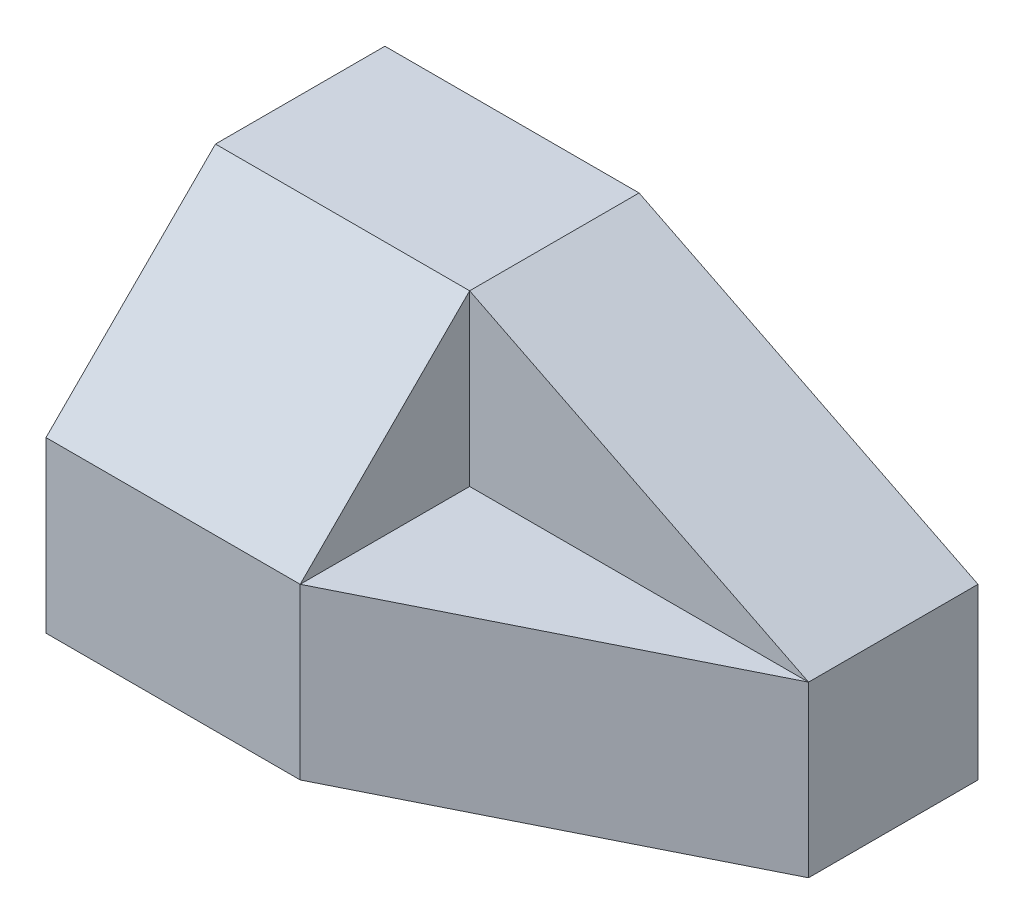
SolidWorks part; units mm, degrees
ref_plane "Front Plane" through (0, 0, 0) normal (0, 0, 1) x (1, 0, 0)
ref_plane "Top Plane" through (0, 0, 0) normal (0, 1, 0) x (1, 0, 0)
ref_plane "Right Plane" through (0, 0, 0) normal (1, 0, 0) x (0, 0, -1)
sketch "Sketch1" plane through (0, 0, 0) normal (0, 1, 0) x (1, 0, 0)
  line L1 (0, 0) -> (177.8, 0)
  line L2 (0, 0) -> (0, 101.6)
  line L3 (0, 101.6) -> (177.8, 101.6)
  line L4 (177.8, 0) -> (177.8, 101.6)
extrude "Boss-Extrude1" add sketch "Sketch1" along normal blind 101.6
sketch "Sketch2" plane through (0, 0, 0) normal (-1, 0, 0) x (0, 0, 1)
  line L1 (-101.6, 101.6) -> (0, 101.6) construction
  line L3 (0, 101.6) -> (0, 0) construction
  line L4 (0, 50.8) -> (-50.8, 101.6)
  line L5 (-50.8, 101.6) -> (0, 101.6)
extrude "Cut-Extrude7" cut sketch "Sketch2" against normal blind 76.2 and the other way through all flip side to cut
sketch "Sketch6" plane through (0, 0, 0) normal (0, 1, 0) x (1, 0, 0)
  line L0 (76.2, 0) -> (177.8, 50.8)
  line L1 (177.8, 0) -> (177.8, 101.6) construction
  line L2 (177.8, 50.8) -> (177.8, 0)
  line L3 (177.8, 0) -> (76.2, 0)
extrude "Cut-Extrude10" cut sketch "Sketch6" along normal blind 50.8
sketch "Sketch7" plane through (177.8, 0, 0) normal (1, 0, 0) x (0, 0, -1)
  line L0 (0, 50.8) -> (50.8, 101.6)
  line L1 (0, 101.6) -> (101.6, 101.6) construction
  line L2 (50.8, 101.6) -> (50.8, 50.8)
  line L3 (50.8, 50.8) -> (101.6, 101.6)
  line L5 (50.8, 101.6) -> (101.6, 101.6)
sketch "Sketch8" plane through (0, 101.6, 0) normal (0, 1, 0) x (1, 0, 0)
  line L0 (76.2, 50.8) -> (177.8, 101.6)
  line L1 (177.8, 101.6) -> (88.9, 101.6)
  line L2 (177.8, 101.6) -> (0, 101.6) construction
  line L3 (88.9, 101.6) -> (76.2, 50.8)
  line L4 (177.8, 101.6) -> (177.8, 0)
  line L5 (177.8, 0) -> (76.2, 0)
  line L6 (76.2, 0) -> (76.2, 50.8)
  line L8 (177.8, 50.8) -> (76.2, 0)
extrude "Cut-Extrude12" cut sketch "Sketch8" against normal blind 101.6 and the other way through all contours L8
sketch "Sketch9" plane through (0, 101.6, 0) normal (0, 1, 0) x (1, 0, 0)
  line L0 (177.8, 101.6) -> (76.2, 50.8)
  line L2 (177.8, 50.8) -> (177.8, 101.6) construction
  line L3 (177.8, 76.2) -> (177.8, 50.8)
  line L4 (177.8, 50.8) -> (76.2, 0)
  line L5 (76.2, 0) -> (76.2, 50.8)
sketch "Sketch11" plane through (0, 101.6, 0) normal (0, 1, 0) x (1, 0, 0)
  line L0 (177.8, 50.8) -> (76.2, 50.8)
  line L1 (76.2, 50.8) -> (76.2, 0)
  line L2 (76.2, 0) -> (177.8, 50.8)
extrude "Cut-Extrude22" cut sketch "Sketch11" against normal blind 50.8
sketch "Sketch15" plane through (0, 0, -50.8) normal (0, 0, 1) x (1, 0, 0)
  line L0 (177.8, 50.8) -> (76.2, 101.6)
  line L1 (76.2, 101.6) -> (177.8, 101.6)
  line L2 (177.8, 101.6) -> (177.8, 50.8)
extrude "Cut-Extrude25" cut sketch "Sketch15" against normal blind 50.8
sketch "Sketch12" plane through (177.8, 0, 0) normal (1, 0, 0) x (0, 0, -1)
sketch "Sketch13" plane through (177.8, 0, 0) normal (1, 0, 0) x (0, 0, -1)
  line L1 (50.8, 101.6) -> (50.8, 50.8)
  line L2 (50.8, 50.8) -> (101.6, 101.6)
  line L4 (101.6, 101.6) -> (50.8, 101.6)
  line L6 (-5.4543, 159.3147) -> (50.8, 50.8)
  point P6 (95.0868, 57.249)
sketch "Sketch14" plane through (0, 0, -50.8) normal (0, 0, 1) x (1, 0, 0)
